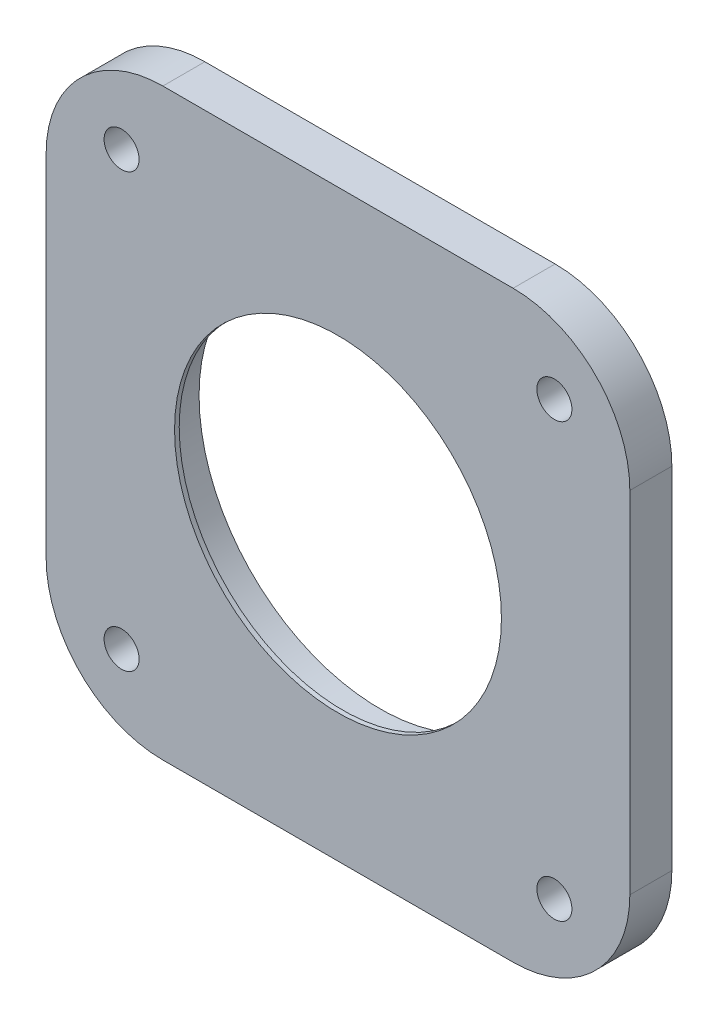
SolidWorks part; units mm, degrees
ref_plane "Front Plane" through (0, 0, 0) normal (0, 0, 1) x (1, 0, 0)
ref_plane "Top Plane" through (0, 0, 0) normal (0, 1, 0) x (1, 0, 0)
ref_plane "Right Plane" through (0, 0, 0) normal (1, 0, 0) x (0, 0, -1)
sketch "Sketch1" plane through (0, 0, 0) normal (0, 0, 1) x (1, 0, 0)
  line L7 (-19.05, -31.75) -> (19.05, -31.75)
  line L8 (-31.75, -19.05) -> (-31.75, 19.05)
  line L9 (-19.05, 31.75) -> (19.05, 31.75)
  line L10 (31.75, -19.05) -> (31.75, 19.05)
  line L11 (-31.75, -31.75) -> (31.75, 31.75) construction
  line L12 (-31.75, 31.75) -> (31.75, -31.75) construction
  circle A0 centre (0, 0) radius 19.685
  arc A1 (-19.05, -31.75) -> (-31.75, -19.05) centre (-19.05, -19.05) cw
  arc A2 (19.05, -31.75) -> (31.75, -19.05) centre (19.05, -19.05) ccw
  arc A3 (19.05, 31.75) -> (31.75, 19.05) centre (19.05, 19.05) cw
  arc A4 (-31.75, 19.05) -> (-19.05, 31.75) centre (-19.05, 19.05) cw
  circle A5 centre (-23.5401, 23.5401) radius 1.905
  circle A6 centre (23.5401, 23.5401) radius 1.905
  circle A7 centre (23.5401, -23.5401) radius 1.905
  circle A8 centre (-23.5401, -23.5401) radius 1.905
  point P21 (-28.0303, 28.0303)
  point P31 (0, 0)
  dimension "D1" = 12.7
  dimension "D2" = 39.37
  dimension "D3" = 6.35
  dimension "D5" = 39.37
  dimension "D4" = 4
extrude "Boss-Extrude1" add sketch "Sketch1" along normal blind 4.572
sketch "Sketch2" plane through (0, 0, 4.572) normal (0, 0, 1) x (1, 0, 0)
  circle A0 centre (0, 0) radius 19.685
  circle A1 centre (0, 0) radius 17.78
  dimension "D1" = 39.37
extrude "Boss-Extrude2" add sketch "Sketch2" against normal blind 0.508
